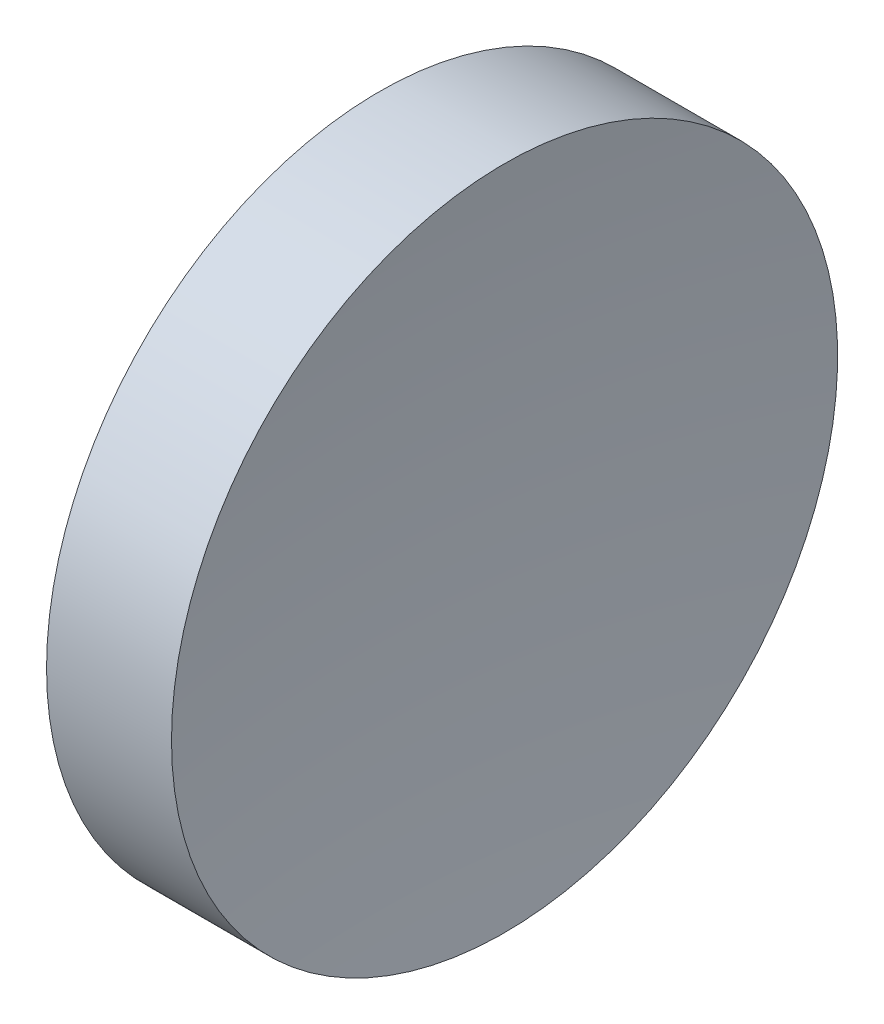
SolidWorks part; units mm, degrees
ref_plane "前视基准面" through (0, 0, 0) normal (0, 0, 1) x (1, 0, 0)
ref_plane "上视基准面" through (0, 0, 0) normal (0, 1, 0) x (1, 0, 0)
ref_plane "右视基准面" through (0, 0, 0) normal (1, 0, 0) x (0, 0, -1)
sketch "草图1" plane through (0, 0, 0) normal (0, 1, 0) x (1, 0, 0)
  line L0 (0, 0) -> (6.9328, 0) construction
  line L1 (0, 0) -> (7.91, 0)
  line L2 (0, 0) -> (0, 25.4)
  line L3 (0, 25.4) -> (9.5295, 25.4)
  arc A0 (9.5295, 25.4) -> (7.91, 0) centre (207.91, 0) ccw
  dimension "D3" = 200
  dimension "D1" = 7.91
  dimension "D2" = 25.4
revolve "旋转1" add sketch "草图1" angle 360 about L0
